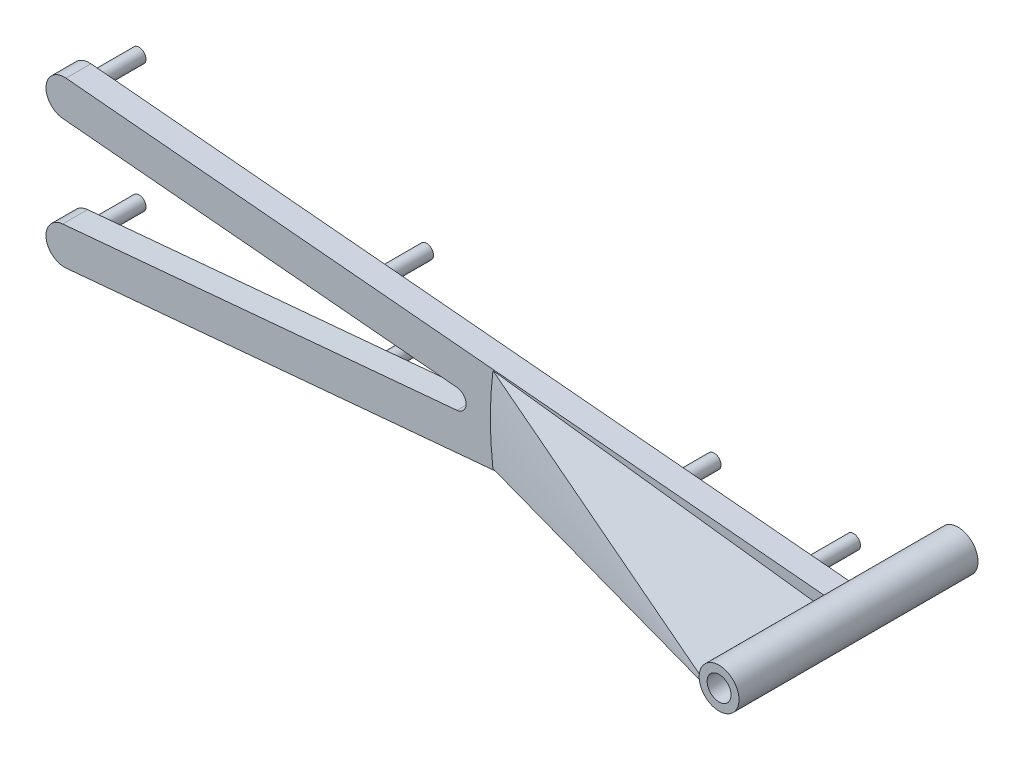
SolidWorks part; units mm, degrees
material "ABS"
ref_plane "Front Plane" through (0, 0, 0) normal (0, 0, 1) x (1, 0, 0)
ref_plane "Top Plane" through (0, 0, 0) normal (0, 1, 0) x (1, 0, 0)
ref_plane "Right Plane" through (0, 0, 0) normal (1, 0, 0) x (0, 0, -1)
curve "Curve4"
  spline degree 3 poles (100, 0, 0) (99.8498, 0.0023, 0) (99.4759, 0.008, 0) (99.1023, 0.0238, 0) (98.8789, 0.0332, 0) knots 0 0 0 0 0.401829 1 1 1 1
curve "Curve5"
  spline degree 3 poles (99.3714, -0.0082, 0) (100.2526, 0, 0) (99.3714, 0.0082, 0) (98.8504, 0.035, 0) (97.904, 0.0811, 0) (96.8285, 0.1543, 0) (95.5159, 0.2583, 0) (94.013, 0.3972, 0) (92.313, 0.574, 0) (90.4281, 0.791, 0) (88.3655, 1.0495, 0) (86.1348, 1.3497, 0) (83.7456, 1.691, 0) (81.2082, 2.0715, 0) (78.5335, 2.4886, 0) (75.7326, 2.9386, 0) (72.8172, 3.4168, 0) (69.799, 3.9177, 0) (66.6904, 4.435, 0) (63.5039, 4.9616, 0) (60.2521, 5.4899, 0) (56.948, 6.0119, 0) (53.6049, 6.519, 0) (50.2363, 7.0024, 0) (46.8558, 7.4534, 0) (43.4774, 7.8632, 0) (40.1152, 8.2232, 0) (36.7837, 8.5249, 0) (33.4975, 8.7606, 0) (30.2716, 8.923, 0) (27.1211, 9.0055, 0) (24.0614, 9.0025, 0) (21.108, 8.909, 0) (18.277, 8.7213, 0) (15.5843, 8.4369, 0) (13.0466, 8.0543, 0) (10.6806, 7.5735, 0) (8.5039, 6.996, 0) (6.5349, 6.3253, 0) (4.7933, 5.5673, 0) (3.3001, 4.7321, 0) (2.0777, 3.8366, 0) (1.1467, 2.91, 0) (0.5165, 2.0014, 0) (0.165, 1.1816, 0) (0.0231, 0.524, 0) (-0.0093, 0, 0) (0.0231, -0.524, 0) (0.165, -1.1816, 0) (0.5165, -2.0014, 0) (1.1467, -2.91, 0) (2.0777, -3.8366, 0) (3.3001, -4.7321, 0) (4.7933, -5.5673, 0) (6.5349, -6.3253, 0) (8.5039, -6.996, 0) (10.6806, -7.5735, 0) (13.0466, -8.0543, 0) (15.5843, -8.4369, 0) (18.277, -8.7213, 0) (21.108, -8.909, 0) (24.0614, -9.0025, 0) (27.1211, -9.0055, 0) (30.2716, -8.923, 0) (33.4975, -8.7606, 0) (36.7837, -8.5249, 0) (40.1152, -8.2232, 0) (43.4774, -7.8632, 0) (46.8558, -7.4534, 0) (50.2363, -7.0024, 0) (53.6049, -6.519, 0) (56.948, -6.0119, 0) (60.2521, -5.4899, 0) (63.5039, -4.9616, 0) (66.6904, -4.435, 0) (69.799, -3.9177, 0) (72.8172, -3.4168, 0) (75.7326, -2.9386, 0) (78.5335, -2.4886, 0) (81.2082, -2.0715, 0) (83.7456, -1.691, 0) (86.1348, -1.3497, 0) (88.3655, -1.0495, 0) (90.4281, -0.791, 0) (92.313, -0.574, 0) (94.013, -0.3972, 0) (95.5159, -0.2583, 0) (96.8285, -0.1543, 0) (97.904, -0.0811, 0) (98.8504, -0.035, 0) (99.3714, -0.0082, 0) (100.2526, 0, 0) (99.3714, 0.0082, 0) knots -0.009667 -0.005395 -0.002168 0 0.002168 0.005395 0.009667 0.014967 0.021271 0.028553 0.036781 0.04592 0.055932 0.066773 0.078397 0.090755 0.103793 0.117456 0.131686 0.146422 0.1616 0.177156 0.193024 0.209135 0.225421 0.241812 0.258238 0.274629 0.290914 0.307025 0.322893 0.338448 0.353626 0.368361 0.38259 0.396253 0.40929 0.421647 0.43327 0.444109 0.454119 0.463255 0.471479 0.478755 0.485052 0.490344 0.49461 0.497833 0.5 0.502167 0.50539 0.509656 0.514948 0.521245 0.528521 0.536745 0.545881 0.555891 0.56673 0.578353 0.59071 0.603747 0.61741 0.631639 0.646374 0.661552 0.677107 0.692975 0.709086 0.725371 0.741762 0.758188 0.774579 0.790865 0.806976 0.822844 0.8384 0.853578 0.868314 0.882544 0.896207 0.909245 0.921603 0.933227 0.944068 0.95408 0.963219 0.971447 0.978729 0.985033 0.990333 0.994605 0.997832 1 1.002168 1.005395 1.009667 periodic
sketch "Sketch2" plane through (0, 0, 0) normal (0, 0, 1) x (1, 0, 0)
  line L0 (100, 0) -> (0, 0) construction
  line L1 (1.2169, -991.9959) -> (1.2169, 49008.0041) construction
  line L2 (93.345, 0) -> (114.935, 0) construction
  line L3 (125.634, 0) -> (131.6629, 0) construction
  line L4 (643.5991, 0) -> (643.5991, -1.016)
  line L9 (0, 0) -> (643.9668, 0)
  line L13 (460.661, 0) -> (473.361, 0)
  circle A0 centre (104.14, 0) radius 10.795 construction
  arc A1 (1.2169, -4.6585) -> (1.2169, 4.6585) centre (9.525, 0) cw
  arc A2 (641.5671, 0) -> (644.1071, 0) centre (642.8371, 0) ccw
  circle A4 centre (104.14, 0) radius 10.795
  circle A9 centre (40.64, 0) radius 12.7
  circle A14 centre (642.3793, 0) radius 1.5875 construction
  arc A15 (642.5108, -1.582) -> (642.5108, 1.582) centre (642.3793, 0) ccw
  spline S2 degree 3 poles (666.3448, -0.0547) (672.2538, 0) (666.3448, 0.0547) (662.8509, 0.2344) (656.505, 0.5436) (649.293, 1.0348) (640.4916, 1.7319) (630.4138, 2.6634) (619.0141, 3.8493) (606.375, 5.3044) (592.5439, 7.0376) (577.5855, 9.0506) (561.5643, 11.3389) (544.5497, 13.8907) (526.6141, 16.6877) (507.8326, 19.7051) (488.2827, 22.9117) (468.0444, 26.2704) (447.1994, 29.739) (425.8316, 33.2703) (404.0263, 36.8132) (381.8707, 40.3133) (359.4533, 43.7135) (336.8645, 46.9554) (314.1962, 49.9798) (291.5418, 52.7277) (268.9963, 55.1412) (246.6566, 57.1646) (224.6209, 58.7452) (202.9892, 59.8341) (181.8631, 60.3875) (161.3458, 60.367) (141.542, 59.7399) (122.5581, 58.4818) (104.5023, 56.5743) (87.485, 54.0089) (71.6197, 50.7848) (57.0237, 46.9125) (43.8205, 42.415) (32.1416, 37.3322) (22.1291, 31.7315) (13.9324, 25.7264) (7.6896, 19.5132) (3.4631, 13.4204) (1.1063, 7.9234) (0.1546, 3.5138) (-0.0622, 0) (0.1546, -3.5138) (1.1063, -7.9234) (3.4631, -13.4204) (7.6896, -19.5132) (13.9324, -25.7264) (22.1291, -31.7315) (32.1416, -37.3322) (43.8205, -42.415) (57.0237, -46.9125) (71.6197, -50.7848) (87.485, -54.0089) (104.5023, -56.5743) (122.5581, -58.4818) (141.542, -59.7399) (161.3458, -60.367) (181.8631, -60.3875) (202.9892, -59.8341) (224.6209, -58.7452) (246.6566, -57.1646) (268.9963, -55.1412) (291.5418, -52.7277) (314.1962, -49.9798) (336.8645, -46.9554) (359.4533, -43.7135) (381.8707, -40.3133) (404.0263, -36.8132) (425.8316, -33.2703) (447.1994, -29.739) (468.0444, -26.2704) (488.2827, -22.9117) (507.8326, -19.7051) (526.6141, -16.6877) (544.5497, -13.8907) (561.5643, -11.3389) (577.5855, -9.0506) (592.5439, -7.0376) (606.375, -5.3044) (619.0141, -3.8493) (630.4138, -2.6634) (640.4916, -1.7319) (649.293, -1.0348) (656.505, -0.5436) (662.8509, -0.2344) (666.3448, -0.0547) (672.2538, 0) (666.3448, 0.0547) knots -0.009667 -0.005395 -0.002168 0 0.002168 0.005395 0.009667 0.014967 0.021271 0.028553 0.036781 0.04592 0.055932 0.066773 0.078397 0.090755 0.103793 0.117456 0.131686 0.146422 0.1616 0.177156 0.193024 0.209135 0.225421 0.241812 0.258238 0.274629 0.290914 0.307025 0.322893 0.338448 0.353626 0.368361 0.38259 0.396253 0.40929 0.421647 0.43327 0.444109 0.454119 0.463255 0.471479 0.478755 0.485052 0.490344 0.49461 0.497833 0.5 0.502167 0.50539 0.509656 0.514948 0.521245 0.528521 0.536745 0.545881 0.555891 0.56673 0.578353 0.59071 0.603747 0.61741 0.631639 0.646374 0.661552 0.677107 0.692975 0.709086 0.725371 0.741762 0.758188 0.774579 0.790865 0.806976 0.822844 0.8384 0.853578 0.868314 0.882544 0.896207 0.909245 0.921603 0.933227 0.944068 0.95408 0.963219 0.971447 0.978729 0.985033 0.990333 0.994605 0.997832 1 1.002168 1.005395 1.009667 only from (670.56, 0) to (670.56, 0)
  point P2 (167.64, 0)
  point P8 (1.2169, -4.6585)
  point P10 (1.2169, 4.6585)
  point P28 (133.9182, 0)
  point P49 (130.0977, 0)
  point P59 (95.1064, 0)
  dimension "D2" = 21.59
  dimension "D3" = 1.016
  dimension "D4" = 1.27
  dimension "D8" = 25.4
  dimension "D9" = 63.5
  dimension "D10" = 3.175
  dimension "D1" = 167.64
  dimension "D6" = 63.5
extrude "Boss-Extrude1" add sketch "Sketch2" along normal blind 5.08
sketch "Sketch3" plane through (0, 0, 5.08) normal (0, 0, 1) x (1, 0, 0)
  line L0 (84.14, -12.7) -> (62.637, -12.7) construction
  line L1 (430.4749, -1041.2705) -> (430.4749, 48958.7295) construction
  line L2 (114.935, 0) -> (641.5671, 0) construction
  line L3 (27.94, 0) -> (0, 0)
  line L4 (641.5671, 0) -> (114.935, 0)
  line L5 (93.345, 0) -> (53.34, 0)
  line L6 (27.94, 0) -> (0, 0)
  line L7 (212.768, -1000) -> (212.768, 49000) construction
  line L8 (93.345, 0) -> (53.34, 0)
  line L9 (224.198, -1000) -> (224.198, 49000) construction
  line L10 (300.8092, -1000) -> (300.8092, 49000) construction
  line L11 (312.2392, -1000) -> (312.2392, 49000) construction
  line L12 (369.7207, -1000) -> (369.7207, 49000) construction
  line L13 (93.345, -17.145) -> (65.0689, -17.145) construction
  line L14 (419.5047, -1000) -> (419.5047, 49000) construction
  line L15 (126.365, -1000) -> (126.365, 49000) construction
  line L16 (381.1507, -1000) -> (381.1507, 49000) construction
  line L17 (52.7726, -27.2676) -> (52.7726, -27.2676) construction
  arc A0 (36.4352, -25.0495) -> (62.637, -12.7) centre (40.64, 0) ccw construction
  circle A2 centre (169.5665, 0) radius 43.2015
  arc A3 (642.5108, -1.582) -> (643.5991, -1.016) centre (642.3793, 0) ccw
  arc A4 (93.345, 0) -> (114.935, 0) centre (104.14, 0) ccw
  arc A5 (27.94, 0) -> (53.34, 0) centre (40.64, 0) ccw
  arc A6 (642.5108, -1.582) -> (643.5991, -1.016) centre (642.3793, 0) ccw
  circle A7 centre (262.5036, 0) radius 38.3056
  arc A8 (27.94, 0) -> (53.34, 0) centre (40.64, 0) ccw
  circle A9 centre (340.9799, 0) radius 28.7408
  circle A10 centre (400.3277, 0) radius 19.177
  circle A11 centre (443.3019, 0) radius 12.827
  circle A12 centre (482.0825, 0) radius 6.477
  arc A13 (52.7726, -27.2676) -> (65.0689, -17.145) centre (40.64, 0) ccw construction
  arc A14 (638.2053, 15.2585) -> (638.2053, 15.2585) centre (638.2053, 15.2585) ccw construction
  arc A18 (641.5671, 0) -> (643.5991, -1.016) centre (642.8371, 0) ccw
  arc A19 (641.5671, 0) -> (643.5991, -1.016) centre (642.8371, 0) ccw
  spline S1 degree 3 poles (1488.1541, -2580.0534) (314.1987, 184.2642) (-15.4092, 68.5977) (1.1063, -7.9234) (3.4631, -13.4204) (7.6896, -19.5132) (13.9324, -25.7264) (22.1291, -31.7315) (32.1416, -37.3322) (43.8205, -42.415) (57.0237, -46.9125) (71.6197, -50.7848) (87.485, -54.0089) (104.5023, -56.5743) (122.5581, -58.4818) (141.542, -59.7399) (161.3458, -60.367) (181.8631, -60.3875) (202.9892, -59.8341) (224.6209, -58.7452) (246.6566, -57.1646) (268.9963, -55.1412) (291.5418, -52.7277) (314.1962, -49.9798) (336.8645, -46.9554) (359.4533, -43.7135) (381.8707, -40.3133) (404.0263, -36.8132) (425.8316, -33.2703) (447.1994, -29.739) (468.0444, -26.2704) (488.2827, -22.9117) (507.8326, -19.7051) (526.6141, -16.6877) (544.5497, -13.8907) (561.5643, -11.3389) (577.5855, -9.0506) (592.5439, -7.0376) (606.375, -5.3044) (619.0141, -3.8493) (630.4138, -2.6634) (754.7119, 8.8252) (895.5191, -9.0089) (-2343.84, -283.812) knots 0.342093 0.342093 0.342093 0.342093 0.502167 0.50539 0.509656 0.514948 0.521245 0.528521 0.536745 0.545881 0.555891 0.56673 0.578353 0.59071 0.603747 0.61741 0.631639 0.646374 0.661552 0.677107 0.692975 0.709086 0.725371 0.741762 0.758188 0.774579 0.790865 0.806976 0.822844 0.8384 0.853578 0.868314 0.882544 0.896207 0.909245 0.921603 0.933227 0.944068 0.95408 0.963219 0.971447 0.978729 1.23227 1.23227 1.23227 1.23227 only from (0, 0) to (642.5108, -1.582)
  spline S2 degree 3 poles (0, 0) (0, -1.0075) (0.1546, -3.5138) (1.1063, -7.9234) (3.4631, -13.4204) (7.6896, -19.5132) (13.9324, -25.7264) (22.1291, -31.7315) (32.1416, -37.3322) (43.8205, -42.415) (57.0237, -46.9125) (71.6197, -50.7848) (87.485, -54.0089) (104.5023, -56.5743) (122.5581, -58.4818) (141.542, -59.7399) (161.3458, -60.367) (181.8631, -60.3875) (202.9892, -59.8341) (224.6209, -58.7452) (246.6566, -57.1646) (268.9963, -55.1412) (291.5418, -52.7277) (314.1962, -49.9798) (336.8645, -46.9554) (359.4533, -43.7135) (381.8707, -40.3133) (404.0263, -36.8132) (425.8316, -33.2703) (447.1994, -29.739) (468.0444, -26.2704) (488.2827, -22.9117) (507.8326, -19.7051) (526.6141, -16.6877) (544.5497, -13.8907) (561.5643, -11.3389) (577.5855, -9.0506) (592.5439, -7.0376) (606.375, -5.3044) (619.0141, -3.8493) (630.4138, -2.6634) (638.0937, -1.9535) (641.9934, -1.6251) (642.5108, -1.582) knots 0.5 0.5 0.5 0.5 0.502167 0.50539 0.509656 0.514948 0.521245 0.528521 0.536745 0.545881 0.555891 0.56673 0.578353 0.59071 0.603747 0.61741 0.631639 0.646374 0.661552 0.677107 0.692975 0.709086 0.725371 0.741762 0.758188 0.774579 0.790865 0.806976 0.822844 0.8384 0.853578 0.868314 0.882544 0.896207 0.909245 0.921603 0.933227 0.944068 0.95408 0.963219 0.971447 0.978729 0.979843 0.979843 0.979843 0.979843
  spline S4 degree 1 poles (52.7726, -27.2676) (638.2053, 15.2585) knots 0 0 1 1 construction
  spline S5 degree 3 poles (52.7726, -27.2676) (54.098, -27.7509) (56.7529, -28.6784) (62.1794, -30.4243) (69.1006, -32.3953) (77.5892, -34.4571) (89.0862, -36.8389) (103.7331, -39.1926) (125.3657, -41.6037) (144.2709, -42.7116) (163.2853, -43.1964) (177.6693, -43.2555) (201.2447, -42.8023) (227.4371, -41.4675) (254.4928, -39.2877) (277.8401, -36.9937) (301.0423, -34.3583) (330.3789, -30.5811) (368.329, -25.1309) (404.83, -19.3409) (435.2358, -14.3425) (451.6826, -11.6119) (464.2574, -9.5208) (476.8398, -7.4307) (497.3171, -4.0443) (526.9629, 0.7645) (562.929, 6.2684) (594.1055, 10.5252) (616.0859, 13.0867) (628.694, 14.3901) (635.0364, 14.9826) (638.2053, 15.2585) knots 0.548481 0.548481 0.548481 0.548481 0.551835 0.555189 0.561898 0.568606 0.575315 0.588731 0.602148 0.62409 0.630798 0.644215 0.655815 0.682649 0.701659 0.715076 0.733763 0.752449 0.779283 0.816817 0.832298 0.845715 0.852722 0.859728 0.873145 0.897318 0.924152 0.950985 0.964402 0.971111 0.977819 0.977819 0.977819 0.977819 construction
  line M19 (641.5671, 0) -> (114.935, 0)
  dimension "D3" = 11.43
  dimension "D7" = 38.354
  dimension "D8" = 25.654
  dimension "D9" = 12.954
  dimension "D4" = 11.43
  dimension "D5" = 11.43
  dimension "D6" = 11.43
  dimension "D1" = 0
  dimension "D10" = 17.145
extrude "Cut-Extrude2" cut sketch "Sketch3" against normal through all both and the other way through all contours A2 M19 | A7 M19 | A9 M19 | A10 M19 | A11 M19 | A12 M19
mirror "Mirror1" about plane through (0, 0, 0) normal (0, 1, 0) of "Cut-Extrude2", "Boss-Extrude1"
sketch "Sketch4" plane through (0, 0, 5.08) normal (0, 0, 1) x (1, 0, 0)
  line L0 (617.4371, -4.0456) -> (617.4371, 4.0456)
  line L1 (617.4371, -1.5056) -> (544.1022, -8.1571) construction
  line L2 (617.6485, -3.837) -> (544.3137, -10.4885)
  line L3 (617.2256, 0.8257) -> (543.8908, -5.8257)
  line L4 (642.8371, 0) -> (617.4371, 0) construction
  line L5 (617.4371, 1.5056) -> (544.1022, 8.1571) construction
  line L6 (617.6485, 3.837) -> (544.3137, 10.4885)
  line L7 (617.2256, -0.8257) -> (543.8908, 5.8257)
  line L8 (642.5108, -1.582) -> (617.6485, -3.837)
  line L9 (642.5108, 1.582) -> (617.6485, 3.837)
  arc A0 (617.6485, -3.837) -> (617.2256, 0.8257) centre (617.4371, -1.5056) ccw
  arc A1 (543.8908, -5.8257) -> (544.3137, -10.4885) centre (544.1022, -8.1571) ccw
  arc A3 (617.6485, 3.837) -> (617.2256, -0.8257) centre (617.4371, 1.5056) cw
  arc A4 (543.8908, 5.8257) -> (544.3137, 10.4885) centre (544.1022, 8.1571) cw
  circle A5 centre (642.8371, 0) radius 1.27
  arc A6 (643.5991, 1.016) -> (642.5108, 1.582) centre (642.3793, 0) ccw construction
  arc A7 (642.5108, -1.582) -> (643.5991, -1.016) centre (642.3793, 0) ccw construction
  arc A8 (643.5991, 1.016) -> (642.5108, 1.582) centre (642.3793, 0) ccw
  arc A9 (642.5108, -1.582) -> (643.5991, -1.016) centre (642.3793, 0) ccw
  spline S0 degree 3 poles (642.5108, 1.582) (641.9934, 1.6251) (638.0937, 1.9535) (630.4138, 2.6634) (619.0141, 3.8493) (606.375, 5.3044) (592.5439, 7.0376) (577.5855, 9.0506) (561.5643, 11.3389) (544.5497, 13.8907) (526.6141, 16.6877) (507.8326, 19.7051) (488.2827, 22.9117) (468.0444, 26.2704) (447.1994, 29.739) (425.8316, 33.2703) (404.0263, 36.8132) (381.8707, 40.3133) (359.4533, 43.7135) (336.8645, 46.9554) (314.1962, 49.9798) (291.5418, 52.7277) (268.9963, 55.1412) (246.6566, 57.1646) (224.6209, 58.7452) (202.9892, 59.8341) (181.8631, 60.3875) (161.3458, 60.367) (141.542, 59.7399) (122.5581, 58.4818) (104.5023, 56.5743) (87.485, 54.0089) (71.6197, 50.7848) (57.0237, 46.9125) (43.8205, 42.415) (32.1416, 37.3322) (22.1291, 31.7315) (13.9324, 25.7264) (7.6896, 19.5132) (3.4631, 13.4204) (1.1063, 7.9234) (0.1546, 3.5138) (-0.0622, 0) (0.1546, -3.5138) (1.1063, -7.9234) (3.4631, -13.4204) (7.6896, -19.5132) (13.9324, -25.7264) (22.1291, -31.7315) (32.1416, -37.3322) (43.8205, -42.415) (57.0237, -46.9125) (71.6197, -50.7848) (87.485, -54.0089) (104.5023, -56.5743) (122.5581, -58.4818) (141.542, -59.7399) (161.3458, -60.367) (181.8631, -60.3875) (202.9892, -59.8341) (224.6209, -58.7452) (246.6566, -57.1646) (268.9963, -55.1412) (291.5418, -52.7277) (314.1962, -49.9798) (336.8645, -46.9554) (359.4533, -43.7135) (381.8707, -40.3133) (404.0263, -36.8132) (425.8316, -33.2703) (447.1994, -29.739) (468.0444, -26.2704) (488.2827, -22.9117) (507.8326, -19.7051) (526.6141, -16.6877) (544.5497, -13.8907) (561.5643, -11.3389) (577.5855, -9.0506) (592.5439, -7.0376) (606.375, -5.3044) (619.0141, -3.8493) (630.4138, -2.6634) (638.0937, -1.9535) (641.9934, -1.6251) (642.5108, -1.582) knots 0.020157 0.020157 0.020157 0.020157 0.021271 0.028553 0.036781 0.04592 0.055932 0.066773 0.078397 0.090755 0.103793 0.117456 0.131686 0.146422 0.1616 0.177156 0.193024 0.209135 0.225421 0.241812 0.258238 0.274629 0.290914 0.307025 0.322893 0.338448 0.353626 0.368361 0.38259 0.396253 0.40929 0.421647 0.43327 0.444109 0.454119 0.463255 0.471479 0.478755 0.485052 0.490344 0.49461 0.497833 0.5 0.502167 0.50539 0.509656 0.514948 0.521245 0.528521 0.536745 0.545881 0.555891 0.56673 0.578353 0.59071 0.603747 0.61741 0.631639 0.646374 0.661552 0.677107 0.692975 0.709086 0.725371 0.741762 0.758188 0.774579 0.790865 0.806976 0.822844 0.8384 0.853578 0.868314 0.882544 0.896207 0.909245 0.921603 0.933227 0.944068 0.95408 0.963219 0.971447 0.978729 0.979843 0.979843 0.979843 0.979843 construction
  point P6 (580.7697, -4.8314)
  point P14 (617.4371, 0)
  point P17 (580.7697, 4.8314)
  dimension "D1" = 25.4
  dimension "D2" = 2.54
sketch "Sketch5" plane through (0, 0, 5.08) normal (0, 0, 1) x (1, 0, 0)
  line L0 (642.5108, -1.582) -> (617.6485, -3.837) construction
  line L1 (642.5108, 1.582) -> (617.6485, 3.837) construction
  line L2 (617.6485, 3.837) -> (544.3137, 10.4885) construction
  line L3 (617.2256, -0.8257) -> (543.8908, 5.8257) construction
  line L4 (617.2256, 0.8257) -> (543.8908, -5.8257) construction
  line L5 (617.6485, -3.837) -> (544.3137, -10.4885) construction
  line L6 (640.9697, -1.7218) -> (617.6485, -3.837)
  line L7 (640.9697, 1.7218) -> (617.6485, 3.837)
  line L8 (617.6485, 3.837) -> (544.3137, 10.4885)
  line L9 (608.1215, 0) -> (543.8908, 5.8257)
  line L10 (608.1215, 0) -> (543.8908, -5.8257)
  line L11 (617.6485, -3.837) -> (544.3137, -10.4885)
  arc A0 (544.3137, 10.4885) -> (543.8908, 5.8257) centre (544.1022, 8.1571) ccw construction
  arc A1 (543.8908, -5.8257) -> (544.3137, -10.4885) centre (544.1022, -8.1571) ccw construction
  arc A2 (544.3137, 10.4885) -> (543.8908, 5.8257) centre (544.1022, 8.1571) ccw
  arc A3 (543.8908, -5.8257) -> (544.3137, -10.4885) centre (544.1022, -8.1571) ccw
  arc A4 (640.9697, -1.7218) -> (640.9697, 1.7218) centre (642.8371, 0) ccw
  dimension "D1" = 5.08
extrude "Boss-Extrude2" add sketch "Sketch5" along normal blind 3.175
sketch "Sketch6" plane through (0, 0, 8.255) normal (0, 0, 1) x (1, 0, 0)
  circle A0 centre (642.8371, 0) radius 2.54
extrude "Boss-Extrude3" add sketch "Sketch6" along normal mid plane 30.48
sketch "Sketch7" plane through (0, 0, 23.495) normal (0, 0, 1) x (1, 0, 0)
  circle A1 centre (642.8371, 0) radius 1.524
  circle A2 centre (642.8371, 0) radius 1.27 construction
  dimension "D1" = 0.254
extrude "Cut-Extrude3" cut sketch "Sketch7" against normal blind 25.4
sketch "Sketch8" plane through (0, 0, 0) normal (0, 0, -1) x (-1, 0, 0)
  arc A1 (-640.9613, -1.7126) -> (-640.9613, 1.7126) centre (-642.8371, 0) ccw
  arc A2 (-640.9613, -1.7126) -> (-640.9613, 1.7126) centre (-642.8371, 0) ccw
  spline S1 degree 3 poles (2297.1172, -297.8307) (-900.2113, -9.6105) (-756.7172, 9.0106) (-630.4138, -2.6634) (-619.0141, -3.8493) (-606.375, -5.3044) (-592.5439, -7.0376) (-577.5855, -9.0506) (-561.5643, -11.3389) (-544.5497, -13.8907) (-526.6141, -16.6877) (-507.8326, -19.7051) (-488.2827, -22.9117) (-468.0444, -26.2704) (-447.1994, -29.739) (-425.8316, -33.2703) (-404.0263, -36.8132) (-381.8707, -40.3133) (-359.4533, -43.7135) (-336.8645, -46.9554) (-314.1962, -49.9798) (-291.5418, -52.7277) (-268.9963, -55.1412) (-246.6566, -57.1646) (-224.6209, -58.7452) (-202.9892, -59.8341) (-181.8631, -60.3875) (-161.3458, -60.367) (-141.542, -59.7399) (-122.5581, -58.4818) (-104.5023, -56.5743) (-87.485, -54.0089) (-71.6197, -50.7848) (-57.0237, -46.9125) (-43.8205, -42.415) (-32.1416, -37.3322) (-22.1291, -31.7315) (-13.9324, -25.7264) (-7.6896, -19.5132) (-3.4631, -13.4204) (-1.1063, -7.9234) (-0.1546, -3.5138) (0.0622, 0) (-0.1546, 3.5138) (-1.1063, 7.9234) (-3.4631, 13.4204) (-7.6896, 19.5132) (-13.9324, 25.7264) (-22.1291, 31.7315) (-32.1416, 37.3322) (-43.8205, 42.415) (-57.0237, 46.9125) (-71.6197, 50.7848) (-87.485, 54.0089) (-104.5023, 56.5743) (-122.5581, 58.4818) (-141.542, 59.7399) (-161.3458, 60.367) (-181.8631, 60.3875) (-202.9892, 59.8341) (-224.6209, 58.7452) (-246.6566, 57.1646) (-268.9963, 55.1412) (-291.5418, 52.7277) (-314.1962, 49.9798) (-336.8645, 46.9554) (-359.4533, 43.7135) (-381.8707, 40.3133) (-404.0263, 36.8132) (-425.8316, 33.2703) (-447.1994, 29.739) (-468.0444, 26.2704) (-488.2827, 22.9117) (-507.8326, 19.7051) (-526.6141, 16.6877) (-544.5497, 13.8907) (-561.5643, 11.3389) (-577.5855, 9.0506) (-592.5439, 7.0376) (-606.375, 5.3044) (-619.0141, 3.8493) (-630.4138, 2.6634) (-763.005, -9.5918) (-914.9973, 11.601) (2179.9395, 330.3883) knots -0.236611 -0.236611 -0.236611 -0.236611 0.021271 0.028553 0.036781 0.04592 0.055932 0.066773 0.078397 0.090755 0.103793 0.117456 0.131686 0.146422 0.1616 0.177156 0.193024 0.209135 0.225421 0.241812 0.258238 0.274629 0.290914 0.307025 0.322893 0.338448 0.353626 0.368361 0.38259 0.396253 0.40929 0.421647 0.43327 0.444109 0.454119 0.463255 0.471479 0.478755 0.485052 0.490344 0.49461 0.497833 0.5 0.502167 0.50539 0.509656 0.514948 0.521245 0.528521 0.536745 0.545881 0.555891 0.56673 0.578353 0.59071 0.603747 0.61741 0.631639 0.646374 0.661552 0.677107 0.692975 0.709086 0.725371 0.741762 0.758188 0.774579 0.790865 0.806976 0.822844 0.8384 0.853578 0.868314 0.882544 0.896207 0.909245 0.921603 0.933227 0.944068 0.95408 0.963219 0.971447 0.978729 1.250221 1.250221 1.250221 1.250221 only from (-640.9613, -1.7126) to (-640.9613, 1.7126)
  spline S2 degree 3 poles (-640.9613, -1.7126) (-640.9605, -1.7126) (-637.5799, -2.001) (-630.4138, -2.6634) (-619.0141, -3.8493) (-606.375, -5.3044) (-592.5439, -7.0376) (-577.5855, -9.0506) (-561.5643, -11.3389) (-544.5497, -13.8907) (-526.6141, -16.6877) (-507.8326, -19.7051) (-488.2827, -22.9117) (-468.0444, -26.2704) (-447.1994, -29.739) (-425.8316, -33.2703) (-404.0263, -36.8132) (-381.8707, -40.3133) (-359.4533, -43.7135) (-336.8645, -46.9554) (-314.1962, -49.9798) (-291.5418, -52.7277) (-268.9963, -55.1412) (-246.6566, -57.1646) (-224.6209, -58.7452) (-202.9892, -59.8341) (-181.8631, -60.3875) (-161.3458, -60.367) (-141.542, -59.7399) (-122.5581, -58.4818) (-104.5023, -56.5743) (-87.485, -54.0089) (-71.6197, -50.7848) (-57.0237, -46.9125) (-43.8205, -42.415) (-32.1416, -37.3322) (-22.1291, -31.7315) (-13.9324, -25.7264) (-7.6896, -19.5132) (-3.4631, -13.4204) (-1.1063, -7.9234) (-0.1546, -3.5138) (0.0622, 0) (-0.1546, 3.5138) (-1.1063, 7.9234) (-3.4631, 13.4204) (-7.6896, 19.5132) (-13.9324, 25.7264) (-22.1291, 31.7315) (-32.1416, 37.3322) (-43.8205, 42.415) (-57.0237, 46.9125) (-71.6197, 50.7848) (-87.485, 54.0089) (-104.5023, 56.5743) (-122.5581, 58.4818) (-141.542, 59.7399) (-161.3458, 60.367) (-181.8631, 60.3875) (-202.9892, 59.8341) (-224.6209, 58.7452) (-246.6566, 57.1646) (-268.9963, 55.1412) (-291.5418, 52.7277) (-314.1962, 49.9798) (-336.8645, 46.9554) (-359.4533, 43.7135) (-381.8707, 40.3133) (-404.0263, 36.8132) (-425.8316, 33.2703) (-447.1994, 29.739) (-468.0444, 26.2704) (-488.2827, 22.9117) (-507.8326, 19.7051) (-526.6141, 16.6877) (-544.5497, 13.8907) (-561.5643, 11.3389) (-577.5855, 9.0506) (-592.5439, 7.0376) (-606.375, 5.3044) (-619.0141, 3.8493) (-630.4138, 2.6634) (-637.5799, 2.001) (-640.9605, 1.7126) (-640.9613, 1.7126) knots 0.021269 0.021269 0.021269 0.021269 0.021271 0.028553 0.036781 0.04592 0.055932 0.066773 0.078397 0.090755 0.103793 0.117456 0.131686 0.146422 0.1616 0.177156 0.193024 0.209135 0.225421 0.241812 0.258238 0.274629 0.290914 0.307025 0.322893 0.338448 0.353626 0.368361 0.38259 0.396253 0.40929 0.421647 0.43327 0.444109 0.454119 0.463255 0.471479 0.478755 0.485052 0.490344 0.49461 0.497833 0.5 0.502167 0.50539 0.509656 0.514948 0.521245 0.528521 0.536745 0.545881 0.555891 0.56673 0.578353 0.59071 0.603747 0.61741 0.631639 0.646374 0.661552 0.677107 0.692975 0.709086 0.725371 0.741762 0.758188 0.774579 0.790865 0.806976 0.822844 0.8384 0.853578 0.868314 0.882544 0.896207 0.909245 0.921603 0.933227 0.944068 0.95408 0.963219 0.971447 0.978729 0.978731 0.978731 0.978731 0.978731
  dimension "D1" = 0
extrude "Cut-Extrude4" cut sketch "Sketch8" against normal up to surface (5.08 mm away) up to face at (636.0315, -2.168, 5.08)
sketch "Sketch9" plane through (0, 0, 5.08) normal (0, 0, -1) x (-1, 0, 0)
  circle A0 centre (-544.1022, 8.1571) radius 0.889
  circle A1 centre (-544.1022, -8.1571) radius 0.889
  circle A2 centre (-580.7697, 4.8314) radius 0.889
  circle A3 centre (-580.7697, -4.8314) radius 0.889
  circle A4 centre (-617.4371, 0) radius 0.889
  circle A5 centre (-635.2171, 0) radius 0.889
  dimension "D1" = 1.778
  dimension "D2" = 17.78
extrude "Boss-Extrude4" add sketch "Sketch9" along normal blind 6.35
fillet "Fillet1" radius 1.27 1 edges at (608.1215, 0, 6.6675)
sketch "Sketch10" plane through (0, 0, 0) normal (0, 1, 0) x (1, 0, 0)
  line L0 (640.2971, -8.255) -> (640.2971, -23.495) construction
  line L1 (640.2971, -8.255) -> (640.2971, -23.495)
  line L2 (640.2971, -8.255) -> (598.4255, -8.255)
  line L3 (640.2971, -23.495) -> (598.4255, -8.255)
  dimension "D1" = 70
sketch3d "3DSketch1"
  line L0 (640.2971, 0, 23.495) -> (598.4255, 0, 8.255) construction
  line L1 (640.2971, 0, 23.495) -> (598.4255, 0, 8.255)
  line L2 (640.2971, 0, 23.495) -> (598.4255, 0, 8.255) construction
  line L3 (640.2971, 0, 23.495) -> (598.4255, 0, 8.255)
  line L4 (640.2971, 0, 8.255) -> (640.2971, 0, 23.495) construction
  line L5 (640.2971, 0, 8.255) -> (598.4255, 0, 8.255) construction
  line L6 (640.2971, 0, 8.255) -> (640.2971, 0, 23.495)
  line L7 (640.2971, 0, 8.255) -> (598.4255, 0, 8.255)
  circle A1 centre (642.8371, 0, 23.495) radius 2.54
  circle A2 centre (642.8371, 0, 23.495) radius 2.54
  point P7 (642.8371, 0, 26.035)
  point P9 (642.8371, 0, 20.955)
  dimension "D1" = 0
revolve "Revolve1" add sketch "Sketch10" angle 7 about axis through (642.8371, 0, -1.905) along (0, 0, 1) other way angle 7
equation "\"0.5n\"=0"
